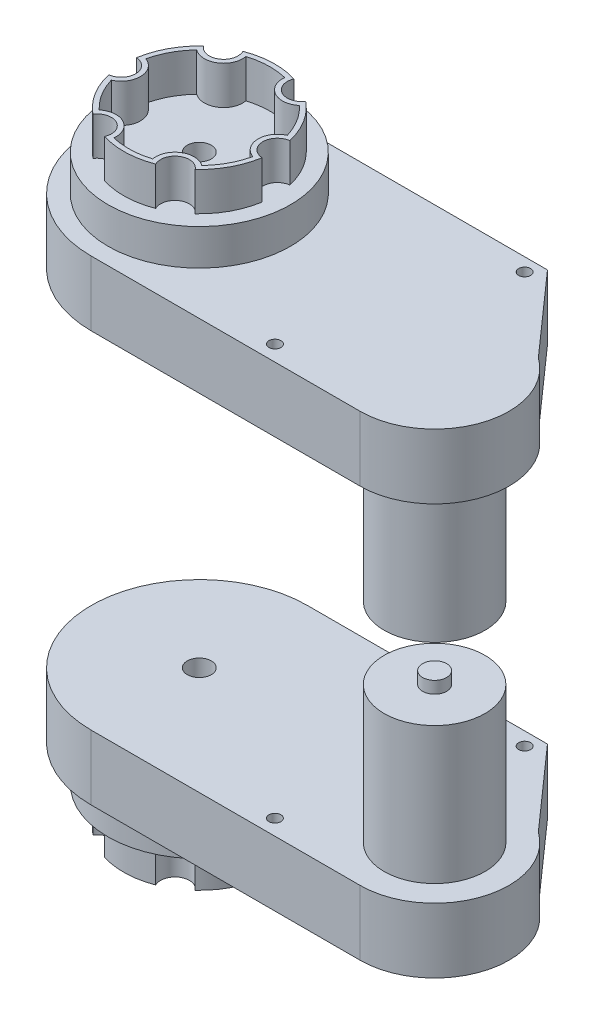
SolidWorks part; units mm, degrees
ref_plane "Front Plane" through (0, 0, 0) normal (0, 0, 1) x (1, 0, 0)
ref_plane "Top Plane" through (0, 0, 0) normal (0, 1, 0) x (1, 0, 0)
ref_plane "Right Plane" through (0, 0, 0) normal (1, 0, 0) x (0, 0, -1)
sketch "Sketch1" plane through (0, 0, 0) normal (0, 1, 0) x (1, 0, 0)
  line L0 (0, 45) -> (100, 45)
  line L1 (100, 45) -> (129.8624, 11.3364)
  line L2 (0, -45) -> (112, -45)
  circle A0 centre (0, 0) radius 45
  circle A1 centre (112, -14) radius 18
  circle A2 centre (112, -14) radius 31
  circle A3 centre (0, 0) radius 5
  circle A4 centre (112, -14) radius 18.5
  circle A5 centre (96, 39.5) radius 2.5
  circle A6 centre (70, -38.5) radius 2.5
  dimension "D2" = 10
  dimension "D3" = 90
  dimension "D4" = 62
  dimension "D5" = 36
  dimension "D6" = 37
  dimension "D7" = 45
  dimension "D9" = 5
  dimension "D12" = 5
  dimension "D1" = 100
  dimension "D8" = 112
  dimension "D10" = 5.5
  dimension "D11" = 96
  dimension "D13" = 70
  dimension "D14" = 6.5
extrude "Boss-Extrude1" add sketch "Sketch1" along normal blind 27 contours A2 L1 L0 A0 L2 A6 A5 | A0 A3 | A2 L1 A4 | A1 | A4 A1
sketch "Sketch2" plane through (0, 27, 0) normal (0, 1, 0) x (1, 0, 0)
  circle A1 centre (112, -14) radius 21
  dimension "D2" = 42
extrude "Boss-Extrude2" add sketch "Sketch2" along normal blind 57
sketch "Sketch4" plane through (0, 0, 0) normal (0, -1, 0) x (1, 0, 0)
  circle A0 centre (0, 0) radius 38
  circle A1 centre (0, 0) radius 33
  dimension "D1" = 76
  dimension "D2" = 66
extrude "Boss-Extrude3" add sketch "Sketch4" along normal blind 15
sketch "Sketch5" plane through (0, -15, 0) normal (0, -1, 0) x (1, 0, 0)
  line L0 (25.4866, -0.8276) -> (-25.4866, 0.8276) construction
  line L1 (13.46, 21.6582) -> (-13.46, -21.6582) construction
  line L2 (12.0266, -22.4858) -> (-12.0266, 22.4858) construction
  line L3 (12.0266, -22.4858) -> (14.8563, -27.7766) construction
  line L4 (25.4866, -0.8276) -> (31.4834, -1.0223) construction
  line L5 (13.46, 21.6582) -> (16.6271, 26.7543) construction
  arc A0 (31.1061, 4.9658) -> (21.3983, 23.1163) centre (0, 0) ccw
  arc A4 (9.3201, -30.0896) -> (19.8536, -24.4558) centre (14.8563, -27.7766) cw
  arc A5 (-31.1061, -4.9658) -> (-30.7184, 6.9734) centre (-31.4834, 1.0223) ccw
  arc A6 (21.3983, 23.1163) -> (11.2526, 29.4216) centre (16.6271, 26.7543) cw
  arc A7 (30.7184, -6.9734) -> (31.1061, 4.9658) centre (31.4834, -1.0223) cw
  arc A8 (-11.2526, -29.4216) -> (-21.3983, -23.1163) centre (-16.6271, -26.7543) ccw
  arc A9 (-19.8536, 24.4558) -> (-9.3201, 30.0896) centre (-14.8563, 27.7766) ccw
  arc A10 (11.2526, 29.4216) -> (-9.3201, 30.0896) centre (0, 0) ccw
  arc A11 (-19.8536, 24.4558) -> (-30.7184, 6.9734) centre (0, 0) ccw
  arc A12 (-31.1061, -4.9658) -> (-21.3983, -23.1163) centre (0, 0) ccw
  arc A13 (-11.2526, -29.4216) -> (9.3201, -30.0896) centre (0, 0) ccw
  arc A14 (19.8536, -24.4558) -> (30.7184, -6.9734) centre (0, 0) ccw
  arc A15 (20.0203, -21.6665) -> (28.2913, -8.3579) centre (0, 0) ccw
  arc A16 (28.2913, -8.3579) -> (28.7739, 6.5048) centre (31.4834, -1.0223) cw
  arc A17 (28.7739, 6.5048) -> (21.3838, 20.322) centre (0, 0) ccw
  arc A18 (21.3838, 20.322) -> (8.7536, 28.1713) centre (16.6271, 26.7543) cw
  arc A19 (8.7536, 28.1713) -> (-6.9075, 28.6799) centre (0, 0) ccw
  arc A20 (-20.0203, 21.6665) -> (-6.9075, 28.6799) centre (-14.8563, 27.7766) ccw
  arc A21 (-20.0203, 21.6665) -> (-28.2913, 8.3579) centre (0, 0) ccw
  arc A22 (-28.7739, -6.5048) -> (-28.2913, 8.3579) centre (-31.4834, 1.0223) ccw
  arc A23 (-28.7739, -6.5048) -> (-21.3838, -20.322) centre (0, 0) ccw
  arc A24 (-8.7536, -28.1713) -> (-21.3838, -20.322) centre (-16.6271, -26.7543) ccw
  arc A25 (-8.7536, -28.1713) -> (6.9075, -28.6799) centre (0, 0) ccw
  arc A26 (6.9075, -28.6799) -> (20.0203, -21.6665) centre (14.8563, -27.7766) cw
  dimension "D3" = 120
  dimension "D4" = 60
  dimension "D6" = 2
extrude "Boss-Extrude4" add sketch "Sketch5" along normal blind 16 and the other way up to surface (15 mm away) other way up to face at (0, 0, 5)
sketch "Sketch6" plane through (0, 84, 0) normal (0, 1, 0) x (1, 0, 0)
  circle A0 centre (112, -14) radius 5
  dimension "D1" = 10
extrude "Boss-Extrude5" add sketch "Sketch6" along normal blind 5
sketch "Sketch7" plane through (0, 0, 0) normal (0, -1, 0) x (1, 0, 0)
  circle A0 centre (0, 0) radius 33
  dimension "D1" = 66
extrude "Boss-Extrude6" add sketch "Sketch7" along normal blind 15
sketch "Sketch8" plane through (0, 27, 0) normal (0, 1, 0) x (1, 0, 0)
  circle A0 centre (0, 0) radius 5 construction
  circle A1 centre (0, 0) radius 5
extrude "Cut-Extrude1" cut sketch "Sketch8" against normal blind 65
ref_plane "Plane1" through (0, 99, 0) normal (0, 1, 0) x (1, 0, 0)
mirror "Mirror2" about plane through (0, 99, 0) normal (0, 1, 0) of bodies 109 105
